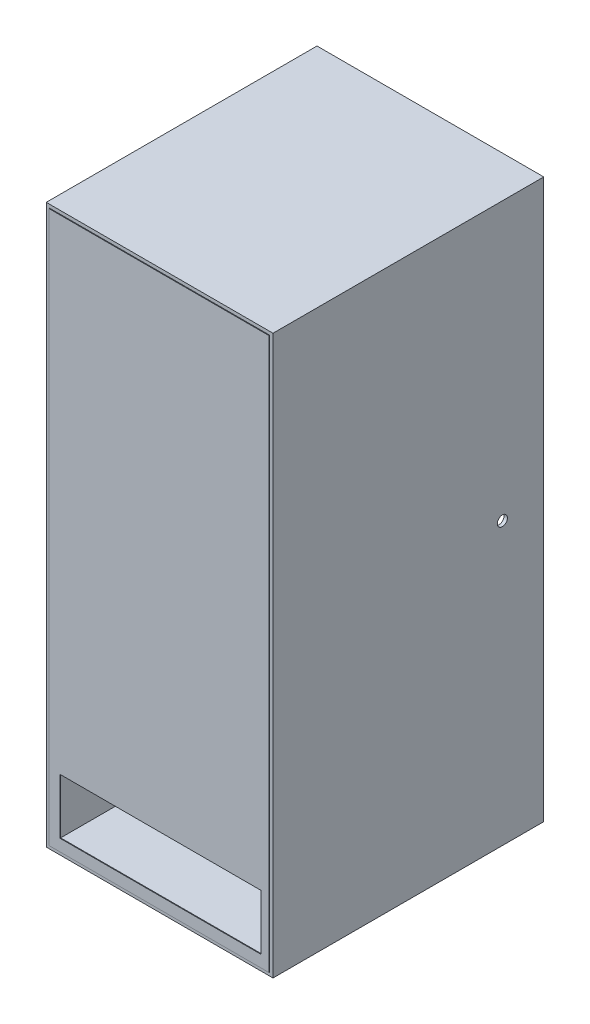
SolidWorks part; units mm, degrees
ref_plane "Front Plane" through (0, 0, 0) normal (0, 0, 1) x (1, 0, 0)
ref_plane "Top Plane" through (0, 0, 0) normal (0, 1, 0) x (1, 0, 0)
ref_plane "Right Plane" through (0, 0, 0) normal (1, 0, 0) x (0, 0, -1)
sketch "Sketch2" plane through (0, 0, 0) normal (0, 0, 1) x (1, 0, 0)
  line L1 (-46.9632, 119.82) -> (18.0368, 119.82)
  line L2 (-46.9632, 119.82) -> (-46.9632, -43.18)
  line L3 (-46.9632, -43.18) -> (18.0368, -43.18)
  line L4 (18.0368, 119.82) -> (18.0368, -43.18)
extrude "Extrude-Thin1" add sketch "Sketch2" along normal blind 80 thin thin type one direction wall 1
sketch "Sketch3" plane through (0, 0, 80) normal (0, 0, 1) x (1, 0, 0)
  line L1 (-46.9632, 119.82) -> (18.0368, 119.82)
  line L2 (-46.9632, 119.82) -> (-46.9632, -43.18)
  line L3 (-46.9632, -43.18) -> (18.0368, -43.18)
  line L4 (18.0368, 119.82) -> (18.0368, -43.18)
extrude "Boss-Extrude1" add sketch "Sketch3" along normal blind 0.2 separate body
sketch "Sketch7" plane through (0, 0, 80.2) normal (0, 0, 1) x (1, 0, 0)
  line L1 (-44.0829, -40.0658) -> (16.0314, -40.0658)
  line L2 (-44.0829, -40.0658) -> (-44.0829, -22.9191)
  line L3 (-44.0829, -22.9191) -> (16.0314, -22.9191)
  line L4 (16.0314, -40.0658) -> (16.0314, -22.9191)
extrude "Extrude-Thin7" add sketch "Sketch7" against normal blind 60 thin
sketch "Sketch8" plane through (0, -21.9191, 0) normal (0, 1, 0) x (1, 0, 0)
  line L0 (17.0314, -20.2) -> (-45.0829, -20.2) construction
  line L1 (-29.1812, -20.2) -> (-5.5736, -20.2)
  line L2 (-29.1812, -20.2) -> (-29.1812, -76.4792)
  line L3 (-29.1812, -76.4792) -> (-5.5736, -76.4792)
  line L4 (-5.5736, -20.2) -> (-5.5736, -76.4792)
extrude "Cut-Extrude1" cut sketch "Sketch8" against normal blind 10
sketch "Sketch9" plane through (0, 0, 80) normal (0, 0, -1) x (-1, 0, 0)
  line L1 (-15.6643, -23.328) -> (43.6933, -23.328)
  line L2 (-15.6643, -23.328) -> (-15.6643, -39.6858)
  line L3 (-15.6643, -39.6858) -> (43.6933, -39.6858)
  line L4 (43.6933, -23.328) -> (43.6933, -39.6858)
extrude "Cut-Extrude2" cut sketch "Sketch9" against normal blind 10
sketch "Sketch10" plane through (19.0368, 0, 0) normal (1, 0, 0) x (0, 0, -1)
  circle A0 centre (-12.2201, 38.9299) radius 1.5
extrude "Cut-Extrude3" cut sketch "Sketch10" against normal blind 20
